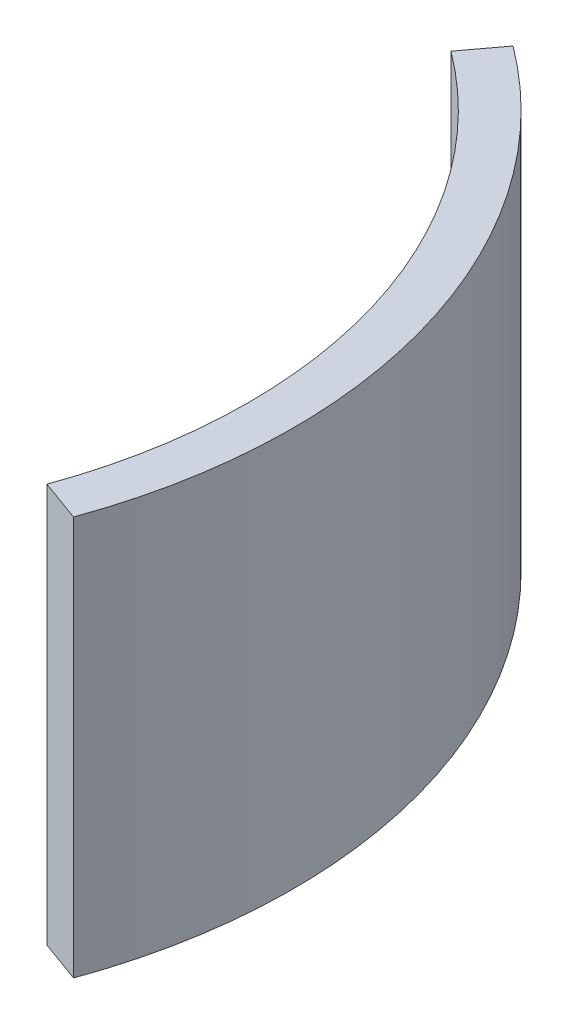
SolidWorks part; units mm, degrees
ref_plane "Front Plane" through (0, 0, 0) normal (0, 0, 1) x (1, 0, 0)
ref_plane "Top Plane" through (0, 0, 0) normal (0, 1, 0) x (1, 0, 0)
ref_plane "Right Plane" through (0, 0, 0) normal (1, 0, 0) x (0, 0, -1)
sketch "Sketch1" plane through (0, 0, 0) normal (0, 1, 0) x (1, 0, 0)
  line L0 (53.6074, -19.3713) -> (58.3098, -21.0705)
  line L1 (34.1112, 45.6664) -> (37.1034, 49.6723)
  arc A0 (53.6074, -19.3713) -> (34.1112, 45.6664) centre (0, 0) ccw
  arc A1 (58.3098, -21.0705) -> (37.1034, 49.6723) centre (0, 0) ccw
  dimension "D1" = 5
extrude "Boss-Extrude1" add sketch "Sketch1" along normal blind 45
